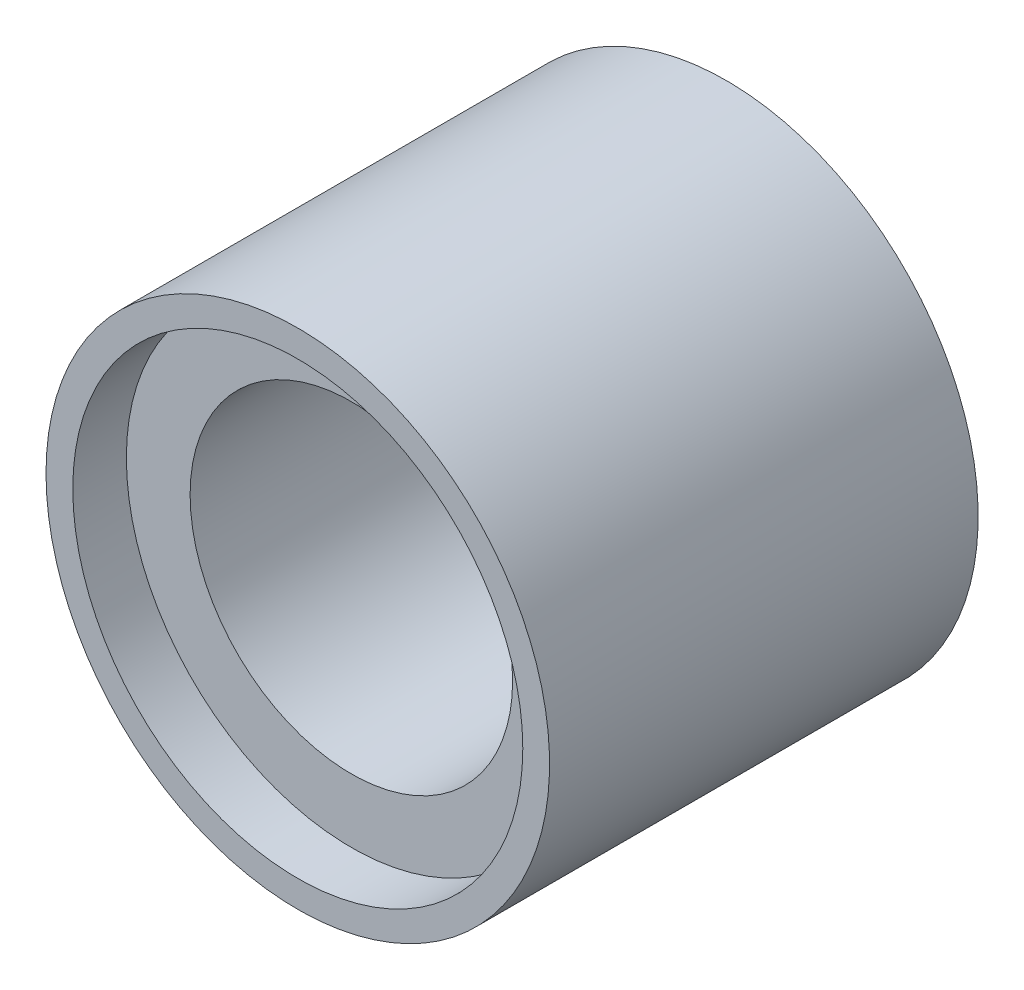
SolidWorks part; units mm, degrees
material "6063-O"
ref_plane "Front Plane" through (0, 0, 0) normal (0, 0, 1) x (1, 0, 0)
ref_plane "Top Plane" through (0, 0, 0) normal (0, 1, 0) x (1, 0, 0)
ref_plane "Right Plane" through (0, 0, 0) normal (1, 0, 0) x (0, 0, -1)
sketch "Sketch1" plane through (0, 0, 0) normal (0, 0, 1) x (1, 0, 0)
  circle A0 centre (0, 0) radius 23.5
  circle A1 centre (0, 0) radius 15.05
  dimension "D1" = 47
  dimension "D2" = 30.1
extrude "Boss-Extrude1" add sketch "Sketch1" along normal mid plane 30
sketch "Sketch2" plane through (0, 0, -15) normal (0, 0, -1) x (-1, 0, 0)
  circle A0 centre (0, 0) radius 21
  circle A1 centre (0, 0) radius 23.5
  dimension "D1" = 47
  dimension "D2" = 42
extrude "Boss-Extrude2" add sketch "Sketch2" along normal blind 5
mirror "Mirror1" about plane through (0, 0, 0) normal (0, 0, 1) of "Boss-Extrude2"
